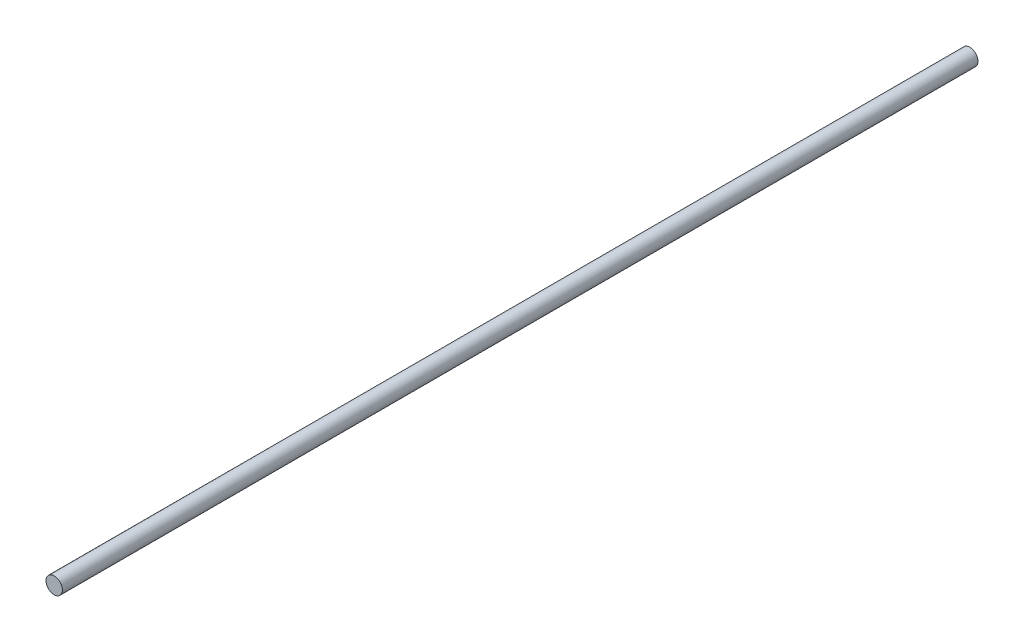
SolidWorks part; units mm, degrees
ref_plane "Plan de face" through (0, 0, 0) normal (0, 0, 1) x (1, 0, 0)
ref_plane "Plan de dessus" through (0, 0, 0) normal (0, 1, 0) x (1, 0, 0)
ref_plane "Plan de droite" through (0, 0, 0) normal (1, 0, 0) x (0, 0, -1)
sketch "Esquisse1" plane through (0, 0, 0) normal (0, 0, 1) x (1, 0, 0)
  circle A0 centre (0, 0) radius 4
  dimension "D1" = 8
extrude "Boss.-Extru.1" add sketch "Esquisse1" along normal blind 448
